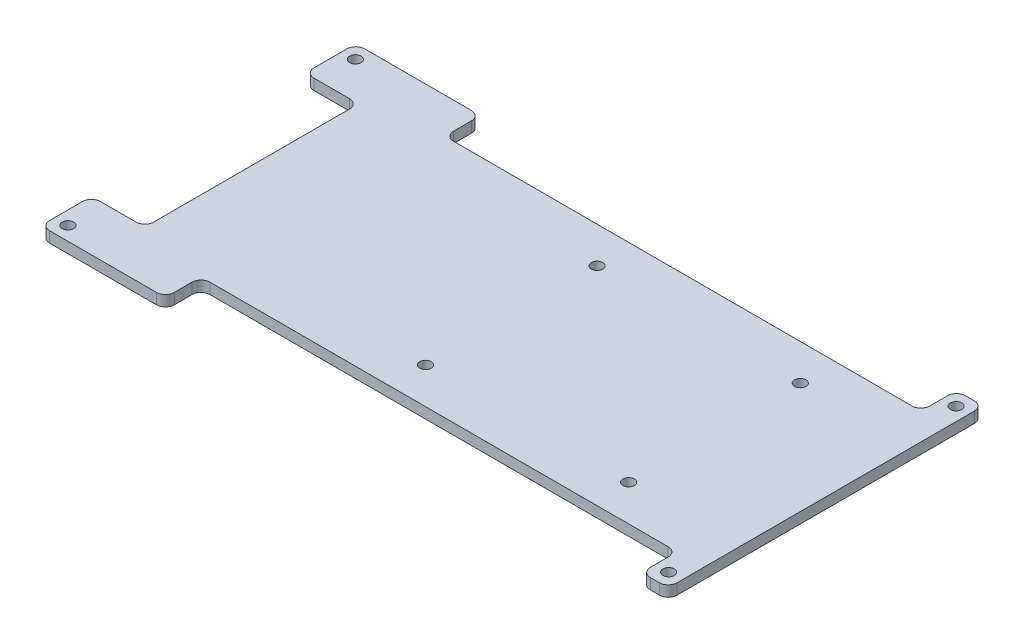
SolidWorks part; units mm, degrees
material "Acrylic (Medium-high impact)"
ref_plane "Front Plane" through (0, 0, 0) normal (0, 0, 1) x (1, 0, 0)
ref_plane "Top Plane" through (0, 0, 0) normal (0, 1, 0) x (1, 0, 0)
ref_plane "Right Plane" through (0, 0, 0) normal (1, 0, 0) x (0, 0, -1)
sketch "Sketch1" plane through (0, 0, 0) normal (0, 1, 0) x (1, 0, 0)
  line L1 (89.535, -44.958) -> (-89.535, -44.958)
  line L2 (89.535, -44.958) -> (89.535, 44.958)
  line L3 (89.535, 44.958) -> (-89.535, 44.958)
  line L4 (-89.535, -44.958) -> (-89.535, 44.958)
  line L5 (89.535, -44.958) -> (-89.535, 44.958) construction
  line L6 (89.535, 44.958) -> (-89.535, -44.958) construction
  point P0 (0, 0)
  dimension "D1" = 89.916
  dimension "D2" = 179.07
extrude "Boss-Extrude1" add sketch "Sketch1" along normal blind 3.0734
hole_wizard "#30 (0.1285) Diameter Hole1" positions "Sketch2" profile "Sketch3" hole size "#30" standard "ANSI Inch" end condition through all
sketch "Sketch2" plane through (0, 3.0734, 0) normal (0, 1, 0) x (1, 0, 0)
  line L0 (-85.725, -41.021) -> (-85.725, 41.021) construction
  line L1 (-85.725, 41.021) -> (85.725, 41.021) construction
  line L2 (85.725, 41.021) -> (85.725, -41.021) construction
  line L3 (85.725, -41.021) -> (-85.725, -41.021) construction
  line L5 (-85.725, 0) -> (-89.535, 0) construction
  line L6 (-89.535, 44.958) -> (-89.535, -44.958) construction
  line L8 (0, 41.021) -> (0, 44.958) construction
  line L9 (89.535, 44.958) -> (-89.535, 44.958) construction
  point P0 (-85.725, 41.021)
  point P2 (-85.725, -41.021)
  point P4 (85.725, -41.021)
  point P6 (85.725, 41.021)
  dimension "D1" = 171.45
  dimension "D2" = 82.042
sketch "Sketch3" plane through (-85.725, 3.0734, -41.021) normal (1, 0, 0) x (0, 0, 1)
  line L0 (0, 0) -> (0, 3.0734)
  line L1 (0, 3.0734) -> (1.6319, 3.0734)
  line L2 (1.6319, 3.0734) -> (1.6319, 0)
  line L5 (1.6319, 0) -> (0, 0)
  line L11 (0, -6.35) -> (0, 107.95) construction
  dimension "Thru Hole Dia." = 3.2639
  dimension "Thru Hole Depth" = 3.0734
hole_wizard "#30 (0.1285) Diameter Hole2" positions "Sketch4" profile "Sketch5" hole size "#30" standard "ANSI Inch" end condition through all
sketch "Sketch4" plane through (0, 3.0734, 0) normal (0, 1, 0) x (1, 0, 0)
  line L0 (-0.215, 24.5) -> (57.785, 24.5) construction
  line L1 (57.785, 24.5) -> (57.785, -24.5) construction
  line L2 (57.785, -24.5) -> (-0.215, -24.5) construction
  line L3 (-0.215, -24.5) -> (-0.215, 24.5) construction
  line L5 (57.785, 0) -> (89.535, 0) construction
  line L6 (89.535, -44.958) -> (89.535, 44.958) construction
  point P0 (-0.215, 24.5)
  point P2 (-0.215, -24.5)
  point P4 (57.785, -24.5)
  point P6 (57.785, 24.5)
  dimension "D1" = 31.75
  dimension "D2" = 58
  dimension "D3" = 49
sketch "Sketch5" plane through (-0.215, 3.0734, -24.5) normal (1, 0, 0) x (0, 0, 1)
  line L0 (0, 0) -> (0, 3.0734)
  line L1 (0, 3.0734) -> (1.6319, 3.0734)
  line L2 (1.6319, 3.0734) -> (1.6319, 0)
  line L5 (1.6319, 0) -> (0, 0)
  line L11 (0, -6.35) -> (0, 107.95) construction
  dimension "Thru Hole Dia." = 3.2639
  dimension "Thru Hole Depth" = 3.0734
sketch "Sketch6" plane through (0, 3.0734, 0) normal (0, 1, 0) x (1, 0, 0)
  line L0 (-89.535, 44.958) -> (-89.535, -44.958) construction
  line L1 (-89.535, 30.48) -> (-74.295, 30.48)
  line L2 (-89.535, 30.48) -> (-89.535, -30.48)
  line L3 (-89.535, -30.48) -> (-74.295, -30.48)
  line L4 (-74.295, 30.48) -> (-74.295, -30.48)
  line L5 (-74.295, 0) -> (-89.535, 0) construction
  line L6 (-89.535, -44.958) -> (89.535, -44.958) construction
  line L7 (-53.975, -44.958) -> (81.915, -44.958)
  line L8 (-53.975, -44.958) -> (-53.975, -34.798)
  line L9 (-53.975, -34.798) -> (81.915, -34.798)
  line L10 (81.915, -44.958) -> (81.915, -34.798)
  line L11 (89.535, 44.958) -> (-89.535, 44.958) construction
  line L12 (-53.975, 44.958) -> (81.915, 44.958)
  line L13 (-53.975, 44.958) -> (-53.975, 34.798)
  line L14 (-53.975, 34.798) -> (81.915, 34.798)
  line L15 (81.915, 44.958) -> (81.915, 34.798)
  line L16 (89.535, -44.958) -> (89.535, 44.958) construction
  line L17 (-53.975, -34.798) -> (-53.975, 34.798) construction
  dimension "D1" = 15.24
  dimension "D2" = 60.96
  dimension "D3" = 10.16
  dimension "D5" = 35.56
  dimension "D6" = 7.62
extrude "Cut-Extrude1" cut sketch "Sketch6" against normal through all
fillet "Fillet2" radius 2.54 16 edges at (-53.975, 1.5367, -34.798) (-53.975, 1.5367, -44.958) (-89.535, 1.5367, -44.958) (-89.535, 1.5367, -30.48) (-74.295, 1.5367, -30.48) (-74.295, 1.5367, 30.48) (-89.535, 1.5367, 30.48) (-89.535, 1.5367, 44.958) (-53.975, 1.5367, 44.958) (-53.975, 1.5367, 34.798) (81.915, 1.5367, 34.798) (81.915, 1.5367, 44.958) (89.535, 1.5367, 44.958) (89.535, 1.5367, -44.958) (81.915, 1.5367, -44.958) (81.915, 1.5367, -34.798)
